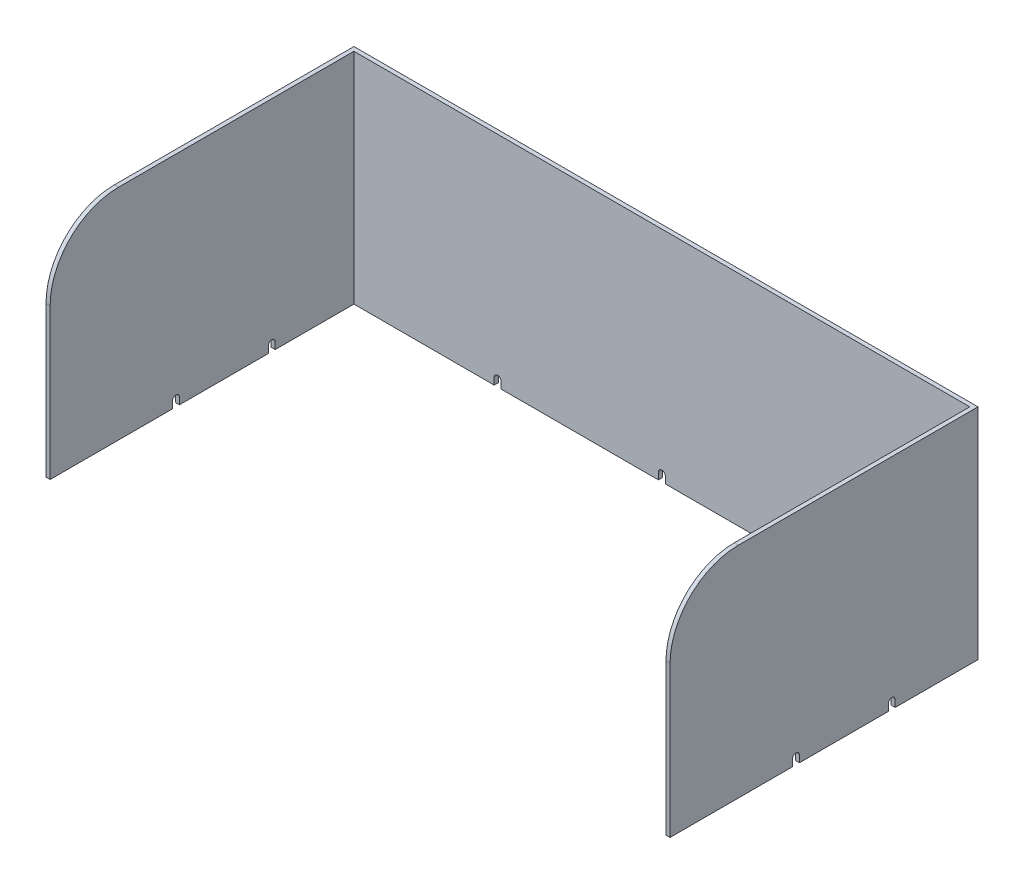
SolidWorks part; units mm, degrees
ref_plane "Alzado" through (0, 0, 0) normal (0, 0, 1) x (1, 0, 0)
ref_plane "Planta" through (0, 0, 0) normal (0, 1, 0) x (1, 0, 0)
ref_plane "Vista lateral" through (0, 0, 0) normal (1, 0, 0) x (0, 0, -1)
sketch "Croquis1" plane through (0, 0, 0) normal (0, 1, 0) x (1, 0, 0)
  line L0 (3, -225) -> (3, -3)
  line L1 (3, -3) -> (453, -3)
  line L2 (453, -3) -> (453, -225)
  line L3 (453, -225) -> (456, -225)
  line L4 (456, -225) -> (456, 0)
  line L5 (456, 0) -> (0, 0)
  line L6 (0, 0) -> (0, -225)
  line L7 (0, -225) -> (3, -225)
  point P2 (0, 0)
  point P10 (4.2203, 117.9881)
  dimension "D1" = 3
  dimension "D2" = 3
  dimension "D3" = 3
  dimension "D4" = 450
  dimension "D5" = 225
extrude "Saliente-Extruir1" add sketch "Croquis1" along normal blind 160
sketch "Croquis2" plane through (0, 0, 0) normal (-1, 0, 0) x (0, 0, 1)
  line L0 (0, 160) -> (0, 0) construction
  line L1 (0, 0) -> (225, 0) construction
  line L2 (60.5, 5) -> (65.5, 5)
  line L3 (60.5, 5) -> (60.5, 0)
  line L4 (60.5, 0) -> (65.5, 0)
  line L5 (65.5, 5) -> (65.5, 0)
  line L7 (130.5, 5) -> (135.5, 5)
  line L8 (130.5, 5) -> (130.5, 0)
  line L9 (130.5, 0) -> (135.5, 0)
  line L10 (135.5, 5) -> (135.5, 0)
  circle A0 centre (63, 5) radius 2.5
  circle A1 centre (133, 5) radius 2.5
  point P16 (0, 0)
  point P17 (0, 0)
  point P18 (64.5, 10.971)
  point P19 (114.5, 10.971)
  line M11 (0, 0) -> (225, 0)
  dimension "D4" = 5
  dimension "D5" = 5
  dimension "D1" = 63
  dimension "D2" = 70
  dimension "D3" = 5
extrude "Cortar-Extruir1" cut sketch "Croquis2" against normal up to surface (456 mm away) contours A0 L3 L5 M11 | L2 A0 | L2 A0 | L7 A1 | A1 L8 L10 M11 | L7 A1 up to face at (456, 80, 112.5)
sketch "Croquis3" plane through (0, 0, 0) normal (0, 0, -1) x (-1, 0, 0)
  line L0 (-456, 0) -> (0, 0) construction
  line L1 (-456, 0) -> (0, 0)
  line L2 (-228, 0) -> (-228, 5) construction
  line L4 (-230.5, 5) -> (-225.5, 5)
  line L5 (-230.5, 5) -> (-230.5, 0)
  line L6 (-230.5, 0) -> (-225.5, 0)
  line L7 (-225.5, 5) -> (-225.5, 0)
  line L8 (-110.5, 5) -> (-105.5, 5)
  line L9 (-110.5, 5) -> (-110.5, 0)
  line L10 (-110.5, 0) -> (-105.5, 0)
  line L11 (-105.5, 5) -> (-105.5, 0)
  line L12 (-350.5, 5) -> (-345.5, 5)
  line L13 (-350.5, 5) -> (-350.5, 0)
  line L14 (-350.5, 0) -> (-345.5, 0)
  line L15 (-345.5, 5) -> (-345.5, 0)
  circle A0 centre (-348, 5) radius 2.5
  circle A1 centre (-228, 5) radius 2.5
  circle A2 centre (-108, 5) radius 2.5
  dimension "D3" = 5
  dimension "D4" = 5
  dimension "D5" = 5
  dimension "D1" = 120
  dimension "D2" = 120
  dimension "D6" = 5
extrude "Cortar-Extruir2" cut sketch "Croquis3" against normal up to next contours L12 A0 | L12 A0 | A0 L13 L1 L15 | L4 A1 | L2 A1 L4 | L2 L6 L7 A1 | A1 L2 L4 | L1 L2 A1 L5 | L8 A2 | L8 A2 | A2 L9 L1 L11
fillet "Redondeo1" radius 50 2 edges at (454.5, 160, 225) (1.5, 160, 225)
